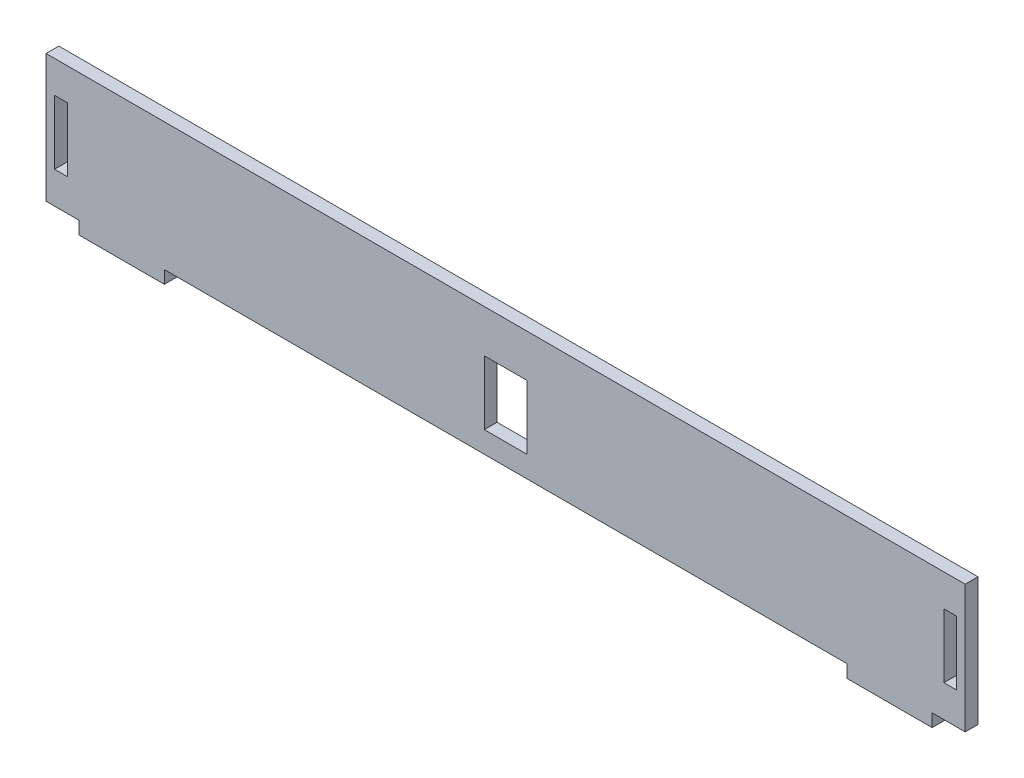
SolidWorks part; units mm, degrees
ref_plane "前视基准面" through (0, 0, 0) normal (0, 0, 1) x (1, 0, 0)
ref_plane "上视基准面" through (0, 0, 0) normal (0, 1, 0) x (1, 0, 0)
ref_plane "右视基准面" through (0, 0, 0) normal (1, 0, 0) x (0, 0, -1)
sketch "草图1" plane through (0, 0, 0) normal (0, 0, 1) x (1, 0, 0)
  line L1 (20, 0) -> (180, 0)
  line L3 (0, 30) -> (200, 30)
  line L6 (0, 0) -> (0, -3)
  line L7 (0, -3) -> (20, -3)
  line L8 (20, 0) -> (20, -3)
  line L10 (200, 0) -> (200, -3)
  line L11 (200, -3) -> (180, -3)
  line L12 (180, 0) -> (180, -3)
  line L13 (200, 30) -> (202.75, 30)
  line L15 (200, 0) -> (202.75, 0)
  line L16 (202.75, 22.5) -> (202.75, 7.5)
  line L17 (202.75, 30) -> (207.75, 30)
  line L19 (202.75, 0) -> (207.75, 0)
  line L20 (207.75, 30) -> (207.75, 0)
  line L21 (202.75, 22.5) -> (205.75, 22.5)
  line L22 (205.75, 22.5) -> (205.75, 7.5)
  line L23 (205.75, 7.5) -> (202.75, 7.5)
  line L25 (0, 30) -> (-2.75, 30)
  line L27 (0, 0) -> (-2.75, 0)
  line L28 (-2.75, 22.5) -> (-2.75, 7.5)
  line L29 (-2.75, 30) -> (-7.75, 30)
  line L31 (-2.75, 0) -> (-7.75, 0)
  line L32 (-7.75, 30) -> (-7.75, 0)
  line L33 (-2.75, 22.5) -> (-5.75, 22.5)
  line L34 (-5.75, 22.5) -> (-5.75, 7.5)
  line L35 (-5.75, 7.5) -> (-2.75, 7.5)
  line L37 (100, 5) -> (105, 5)
  line L38 (105, 5) -> (105, 20)
  line L39 (105, 20) -> (95, 20)
  line L40 (95, 20) -> (95, 5)
  line L41 (95, 5) -> (100, 5)
extrude "凸台-拉伸1" add sketch "草图1" along normal blind 3
